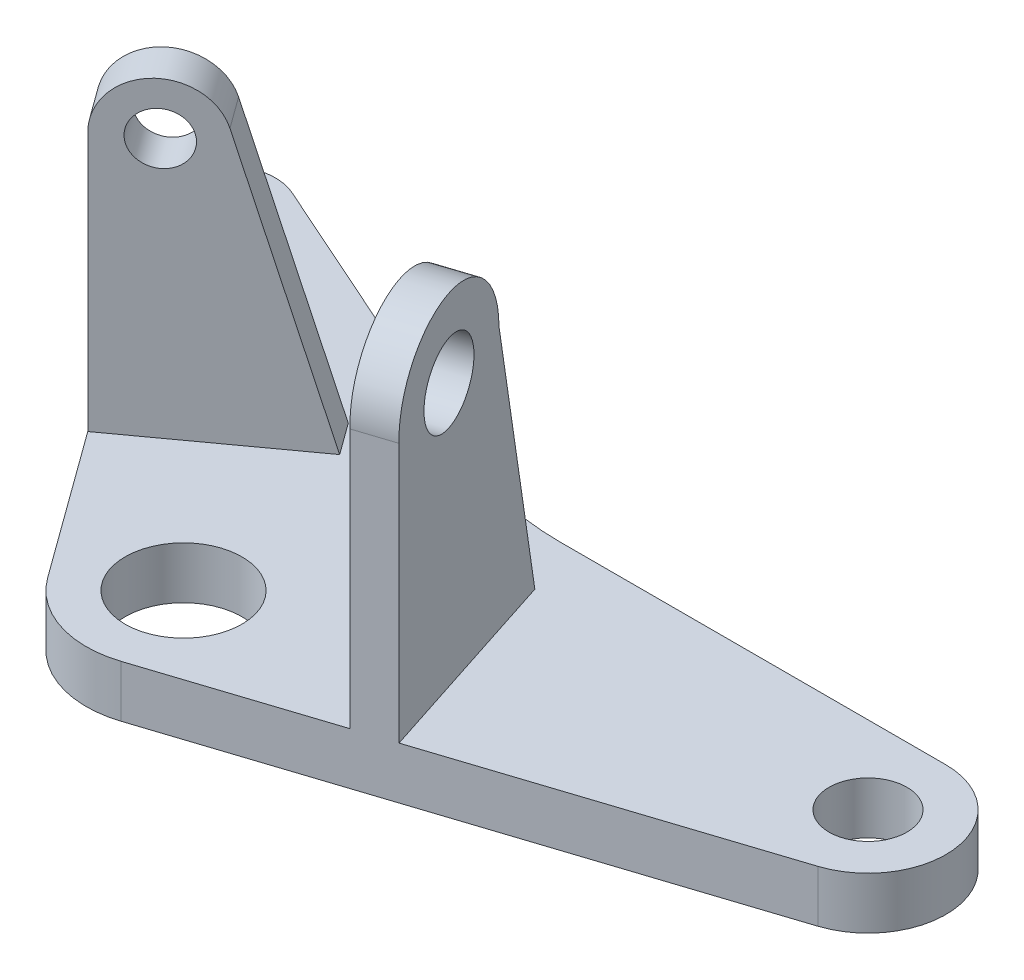
SolidWorks part; units mm, degrees
ref_plane "Front Plane" through (0, 0, 0) normal (0, 0, 1) x (1, 0, 0)
ref_plane "Top Plane" through (0, 0, 0) normal (0, 1, 0) x (1, 0, 0)
ref_plane "Right Plane" through (0, 0, 0) normal (1, 0, 0) x (0, 0, -1)
sketch "Sketch2" plane through (0, 0, 0) normal (0, 1, 0) x (1, 0, 0)
  line L0 (14.7737, 0) -> (74.2481, 0)
  line L1 (77.9563, -23.4127) -> (-3.1166, -49.7549)
  line L2 (-2.3093, 3.6311) -> (-52.498, 25.9766)
  line L3 (-62.224, 13.9659) -> (-19.8871, -44.3058)
  arc A0 (77.9563, -23.4127) -> (74.2481, 0) centre (74.2481, -12) ccw
  arc A1 (-19.8871, -44.3058) -> (-3.1166, -49.7549) centre (-7.7519, -35.489) ccw
  arc A2 (-52.498, 25.9766) -> (-62.224, 13.9659) centre (-55.7519, 18.6682) ccw
  arc A3 (14.7737, 0) -> (-2.3093, 3.6311) centre (14.7737, 42) cw
  dimension "D2" = 24
  dimension "D4" = 30
  dimension "D6" = 16
  dimension "D7" = 42
  dimension "D1" = 18
  dimension "D3" = 24
  dimension "D5" = 54
  dimension "D8" = 82
  dimension "D9" = 48
extrude "Boss-Extrude1" add sketch "Sketch2" along normal blind 8
sketch "Sketch3" plane through (0, 8, 0) normal (0, 1, 0) x (1, 0, 0)
  circle A0 centre (74.2481, -12) radius 6
  circle A1 centre (-55.7519, 18.6682) radius 4
  circle A2 centre (-7.7519, -35.489) radius 9
  dimension "D1" = 8
  dimension "D2" = 12
extrude "Cut-Extrude1" cut sketch "Sketch3" against normal blind 34
sketch "Sketch4" plane through (0, 8, 0) normal (0, 1, 0) x (1, 0, 0)
  line L0 (29.2193, -39.2483) -> (23.4628, -21.5316)
  line L1 (-3.1166, -49.7549) -> (77.9563, -23.4127) construction
  line L2 (-39.8718, -16.7992) -> (-23.3168, -4.7713)
  line L3 (-62.224, 13.9659) -> (-19.8871, -44.3058) construction
  circle A0 centre (-7.7519, -35.489) radius 9
  dimension "D1" = 34
  dimension "D2" = 34
ref_plane "Plane1" through (14.8943, 0, -4.8395) normal (0.9511, 0, -0.309) x (-0.309, 0, -0.9511)
sketch "Sketch5" plane through (14.8943, 0, -4.8395) normal (0.9511, 0, -0.309) x (-0.309, 0, -0.9511)
  line L0 (-46.3566, 8) -> (-46.3566, 48)
  line L1 (-13.7546, 8) -> (-22.368, 48.5227)
  line L2 (-22.9439, 8) -> (-4.5653, 8) construction
  line L3 (-46.3566, 8) -> (-13.7546, 8)
  arc A0 (-22.368, 48.5227) -> (-46.3566, 48) centre (-34.368, 48.5227) ccw
  circle A1 centre (-34.368, 48.5227) radius 6
  dimension "D2" = 24
  dimension "D1" = 40
  dimension "D3" = 12
extrude "Boss-Extrude2" add sketch "Sketch5" against normal blind 6
ref_plane "Plane2" through (-5.7869, 0, -7.965) normal (0.5878, 0, 0.809) x (0.809, 0, -0.5878)
sketch "Sketch6" plane through (-5.7869, 0, -7.965) normal (0.5878, 0, 0.809) x (0.809, 0, -0.5878)
  line L0 (-42.1313, 8) -> (-42.1313, 46)
  line L1 (-42.1313, 8) -> (-21.6682, 8) construction
  line L2 (-42.1313, 8) -> (-42.1313, 0) construction
  line L3 (-26.4412, 50.2051) -> (-14.3391, 8)
  line L4 (-18.1313, 8) -> (-36.1313, 8) construction
  line L5 (-42.1313, 8) -> (-14.3391, 8)
  line L6 (-42.1313, 46) -> (-42.1313, 48)
  arc A0 (-26.4412, 50.2051) -> (-42.1313, 48) centre (-34.1313, 48) ccw
  circle A1 centre (-34.1313, 48) radius 4
  dimension "D2" = 16
  dimension "D4" = 8
  dimension "D1" = 38
  dimension "D3" = 16
extrude "Boss-Extrude3" add sketch "Sketch6" along normal blind 6
